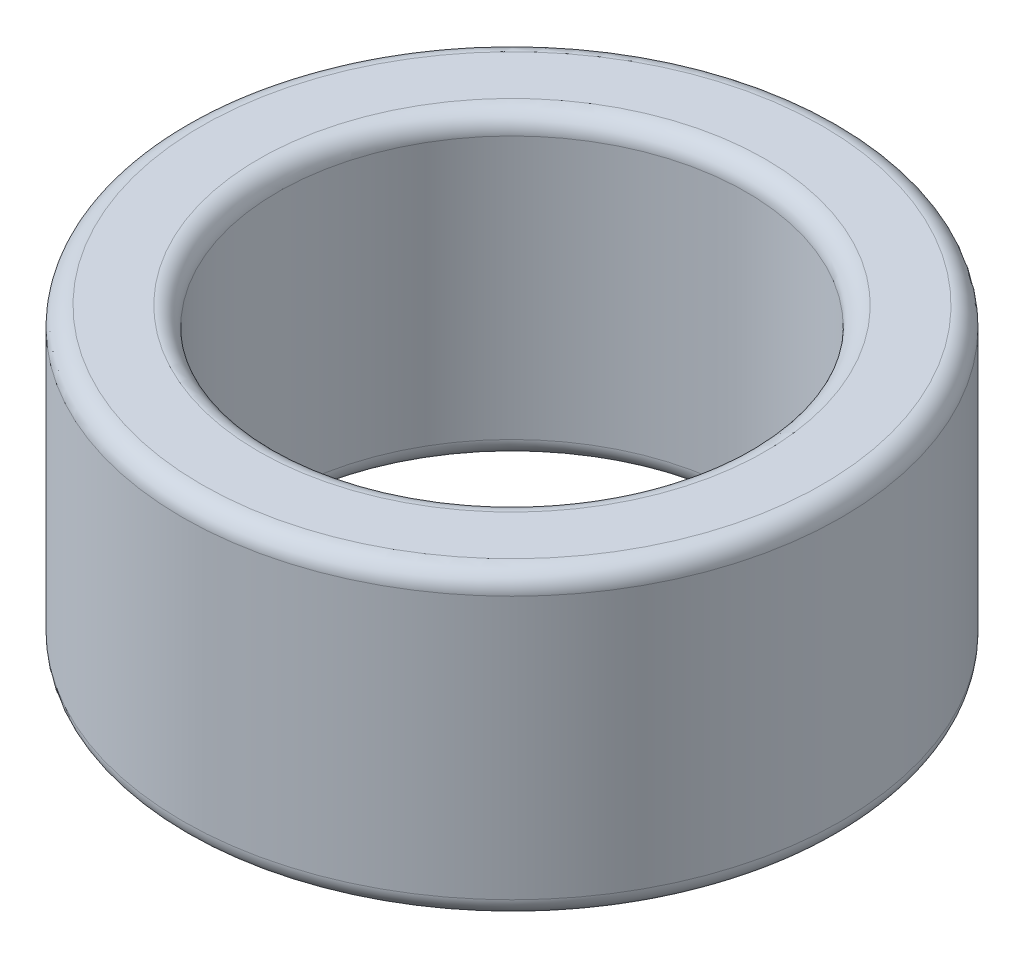
SolidWorks part; units mm, degrees
ref_plane "Front Plane" through (0, 0, 0) normal (0, 0, 1) x (1, 0, 0)
ref_plane "Top Plane" through (0, 0, 0) normal (0, 1, 0) x (1, 0, 0)
ref_plane "Right Plane" through (0, 0, 0) normal (1, 0, 0) x (0, 0, -1)
other "Bounding Box"
ref_plane "Default Plane" through (13.8565, 3.175, 6.7999) normal (0, -1, 0) x (-1, 0, 0)
sketch "Sketch1" plane through (0, 0, 0) normal (0, 1, 0) x (1, 0, 0)
  circle A0 centre (0, 0) radius 1.5621
  circle A1 centre (0, 0) radius 2.1971
  dimension "D1" = 3.1242
  dimension "D2" = 0.635
extrude "Boss-Extrude1" add sketch "Sketch1" along normal blind 2.0066
fillet "Fillet1" radius 0.127 4 edges at (0, 2.0066, 1.5621) (0, 2.0066, 2.1971) (0, 0, 1.5621) (0, 0, 2.1971)
